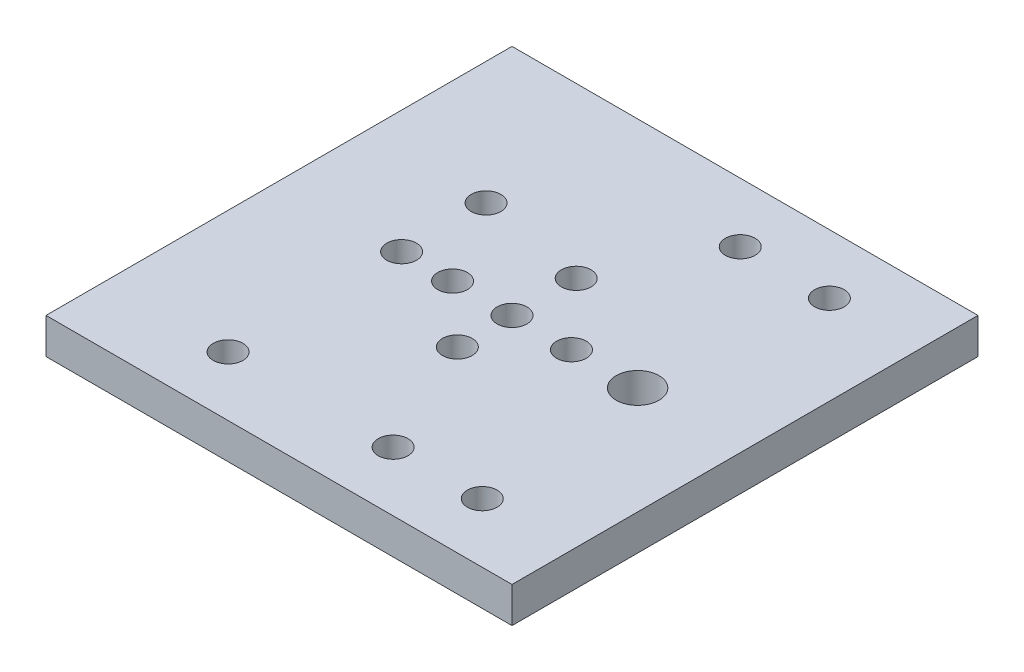
SolidWorks part; units mm, degrees
ref_plane "Front Plane" through (0, 0, 0) normal (0, 0, 1) x (1, 0, 0)
ref_plane "Top Plane" through (0, 0, 0) normal (0, 1, 0) x (1, 0, 0)
ref_plane "Right Plane" through (0, 0, 0) normal (1, 0, 0) x (0, 0, -1)
sketch "Sketch1" plane through (0, 0, 0) normal (0, 1, 0) x (1, 0, 0)
  line L0 (61.5066, 19.404) -> (61.5066, -38.9945) construction
  line L1 (1.1762, 29.404) -> (79.5747, 29.404) construction
  line L2 (1.1762, 29.404) -> (1.1762, -48.9945) construction
  line L3 (1.1762, -48.9945) -> (79.5747, -48.9945) construction
  line L4 (79.5747, 29.404) -> (79.5747, -48.9945) construction
  line L5 (1.1762, 29.404) -> (79.5747, -48.9945) construction
  line L6 (1.1762, -48.9945) -> (79.5747, 29.404) construction
  line L7 (49.5747, 19.404) -> (64.5747, 19.404) construction
  line L8 (64.5747, -38.9945) -> (79.5747, -38.9945) construction
  line L9 (79.5747, -48.9945) -> (79.5747, 29.404)
  line L10 (1.1762, 29.404) -> (79.5747, 29.404)
  line L11 (1.1762, 29.404) -> (1.1762, -48.9945)
  line L12 (49.5747, -38.9945) -> (64.5747, -38.9945) construction
  line L13 (1.1762, -48.9945) -> (79.5747, -48.9945)
  line L14 (64.5747, 19.404) -> (79.5747, 19.404) construction
  circle A0 centre (21.8066, 4.404) radius 2.5
  circle A1 centre (21.8066, -38.9945) radius 2.5
  circle A2 centre (64.5747, 19.404) radius 2.5
  circle A3 centre (49.5747, 19.404) radius 2.5
  circle A4 centre (61.5066, -9.7953) radius 3.6
  circle A5 centre (40.3754, -9.7953) radius 2.5
  circle A6 centre (30.3754, -9.7953) radius 2.5
  circle A7 centre (21.8066, -9.7953) radius 2.5
  circle A8 centre (50.3754, -9.7953) radius 2.5
  circle A9 centre (64.5747, -38.9945) radius 2.5
  circle A10 centre (49.5747, -38.9945) radius 2.5
  circle A11 centre (40.3754, -18.9945) radius 2.5
  circle A12 centre (40.3754, 1.0055) radius 2.5
  point P0 (40.3754, -9.7953)
  point P15 (61.5066, -9.7953)
  dimension "D1" = 5
  dimension "D5" = 10
  dimension "D7" = 15
  dimension "D12" = 5
  dimension "D2" = 10
  dimension "D3" = 10
  dimension "D4" = 10
  dimension "D6" = 10
  dimension "D8" = 25
  dimension "D9" = 8.5688
  dimension "D10" = 11.1312
extrude "Boss-Extrude1" add sketch "Sketch1" along normal blind 6
